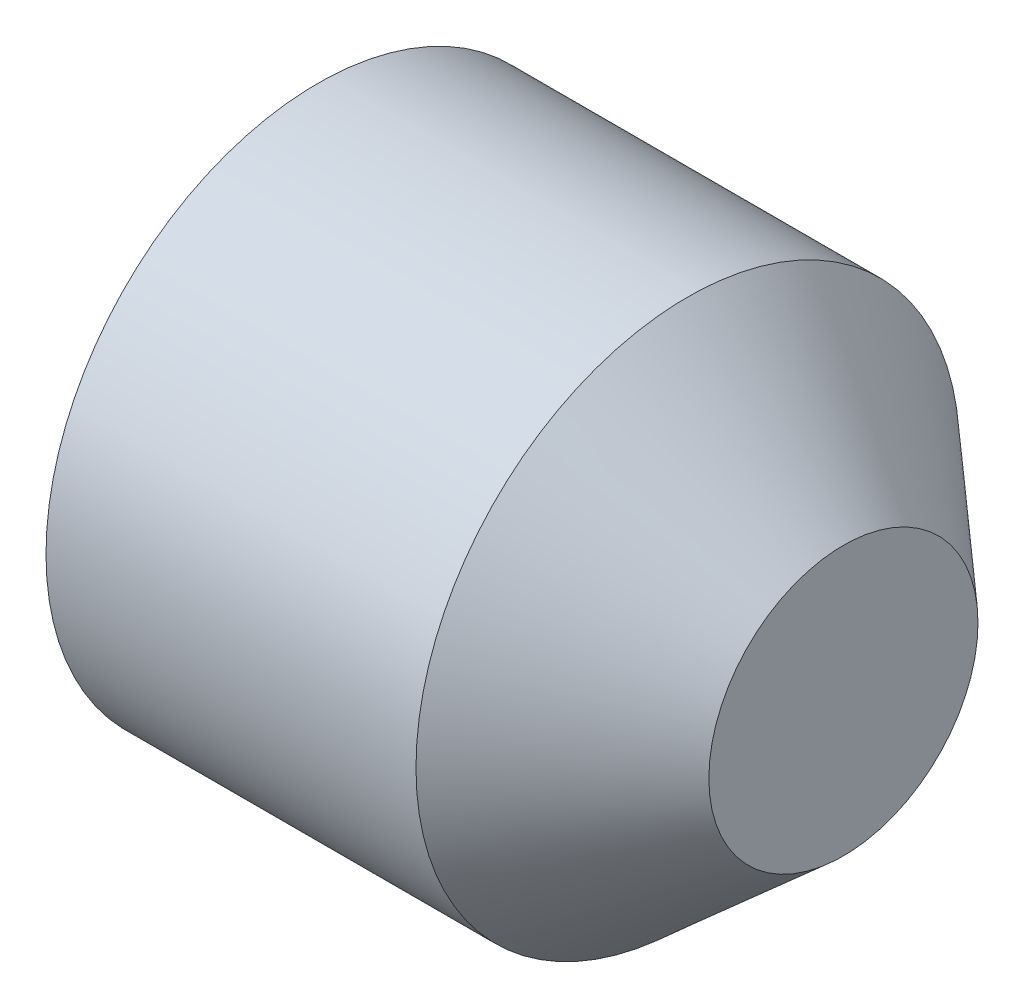
SolidWorks part; units mm, degrees
ref_plane "Front Plane" through (0, 0, 0) normal (0, 0, 1) x (1, 0, 0)
ref_plane "Top Plane" through (0, 0, 0) normal (0, 1, 0) x (1, 0, 0)
ref_plane "Right Plane" through (0, 0, 0) normal (1, 0, 0) x (0, 0, -1)
sketch "Sketch1" plane through (0, 0, 0) normal (0, 0, 1) x (1, 0, 0)
  line L0 (0, 0) -> (356.9849, 0) construction
  line L5 (0, 50) -> (67, 50)
  line L6 (67, 50) -> (67, 150)
  line L7 (67, 150) -> (271.1343, 150)
  line L8 (271.1343, 150) -> (356.9849, 74.2495)
  line L11 (0, 50) -> (0, 0)
  line L13 (0, 0) -> (356.9849, 0)
  line L16 (356.9849, 74.2495) -> (356.9849, 0)
  dimension "D1" = 50
revolve "Revolve1" add sketch "Sketch1" angle 360 about L0
ref_plane "Plane2" through (0, 50, 0) normal (0, 1, 0) x (1, 0, 0)
ref_plane "Plane3" through (0, 0, 0) normal (-1, 0, 0) x (0, 0, 1)
ref_plane "Plane4" through (25, 0, 0) normal (-1, 0, 0) x (0, 0, 1)
sketch "Sketch3" plane through (0, 0, 0) normal (-1, 0, 0) x (0, 0, 1)
  line L0 (0, -999.75) -> (0, 0.25) construction
  line L3 (-1, 24.8425) -> (-2.4465, 52.443)
  line L4 (1, 24.8425) -> (2.4465, 52.443)
  line L6 (0, 24.8425) -> (0, 1049.75) construction
  line L7 (-1, 24.8425) -> (1, 24.8425)
  arc A6 (2.4465, 52.443) -> (-2.4465, 52.443) centre (0, 0) ccw
  dimension "D2" = 2
  dimension "D1" = 3
  dimension "D3" = 105
sketch "Sketch12" plane through (25, 0, 0) normal (-1, 0, 0) x (0, 0, 1)
  line L0 (-9.5068, 22.9515) -> (-20.823, 50.2711) construction
  line L1 (0, -200999.75) -> (0, 0.25) construction
  line L2 (-22.3398, 46.9567) -> (-10.6617, 22.4731)
  line L3 (-17.4068, 49) -> (-8.352, 23.4298)
  line L5 (-10.6617, 22.4731) -> (-8.352, 23.4298)
  arc A0 (-17.4068, 49) -> (-22.3398, 46.9567) centre (0, 0) ccw
  dimension "D2" = 2.5
  dimension "D3" = 104
  dimension "D1" = 22.5
  dimension "D4" = 3
ref_plane "Plane6" through (0, 50, 0) normal (0, 1, 0) x (1, 0, 0)
sketch "Sketch9" plane through (0, 50, 0) normal (0, 1, 0) x (1, 0, 0)
  circle A0 centre (35, 0) radius 1.61
  dimension "D1" = 3.22
  dimension "D2" = 35
extrude "Boss-Extrude1" add sketch "Sketch9" along normal blind 3 separate body
pattern_circular "CirPattern5" count 12 over 360 about axis through (0, 0, 0) along (1, 0, 0) of bodies 202
loft "Cut-Loft1" cut profiles "Sketch3", "Sketch12"
pattern_circular "CirPattern6" count 12 over 360 of "Cut-Loft1"
ref_plane "Plane1" through (0, 53, 0) normal (0, 1, 0) x (1, 0, 0)
